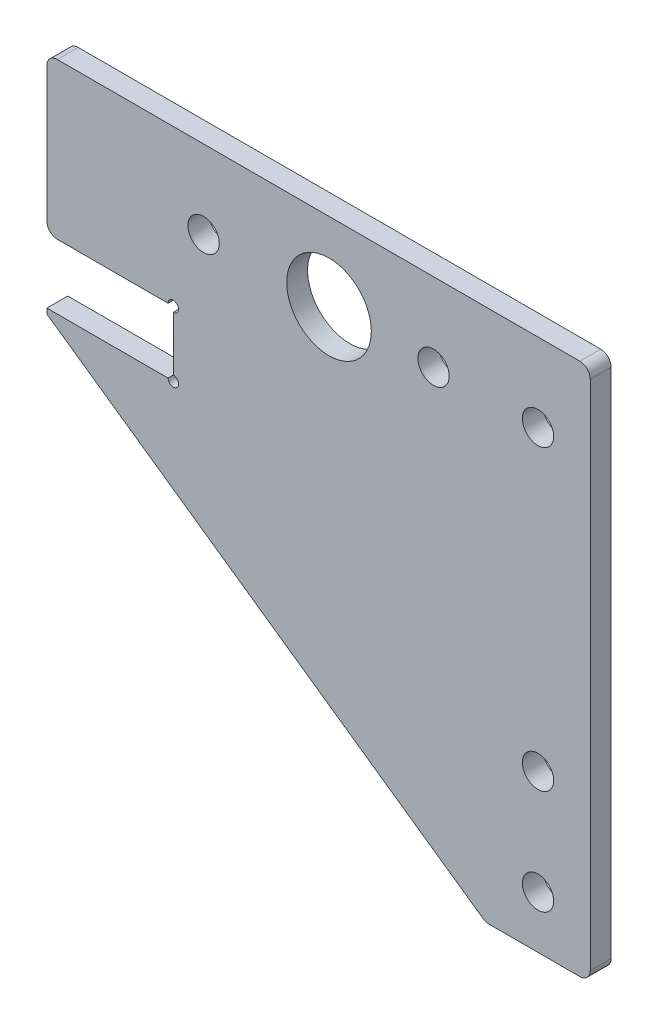
SolidWorks part; units mm, degrees
material "环氧板3240"
ref_plane "前视基准面" through (0, 0, 0) normal (0, 0, 1) x (1, 0, 0)
ref_plane "上视基准面" through (0, 0, 0) normal (0, 1, 0) x (1, 0, 0)
ref_plane "右视基准面" through (0, 0, 0) normal (1, 0, 0) x (0, 0, -1)
other "Configuration Table"
sketch "草图1" plane through (0, 0, 0) normal (0, 0, 1) x (1, 0, 0)
  line L1 (-5, -43.5) -> (5, -43.5)
  line L2 (5, -43.5) -> (5, 7.5)
  line L5 (-47, 7.5) -> (-47, -7.4)
  line L6 (-47, 0) -> (0, 0) construction
  line L7 (0, 0) -> (0, -43.5) construction
  line L9 (-47, -14.0913) -> (-5, -43.5)
  line L10 (-49.5736, -19.2913) -> (-15.2583, -43.3192) construction
  line L11 (-49.5736, -19.2913) -> (-15.2583, -43.3192) construction
  line L14 (-47, -7.4) -> (-34.9, -7.4)
  line L15 (5, 7.5) -> (-47, 7.5)
  line L16 (-34.9, -7.4) -> (-34.9, -13.6)
  line L17 (-34.9, -13.6) -> (-47, -13.6)
  line L18 (-47, -13.6) -> (-47, -14.0913)
  circle A0 centre (-32, 0) radius 1.5
  circle A4 centre (-10, 0) radius 1.5
  circle A5 centre (0, -28.5) radius 1.5
  circle A6 centre (0, 0) radius 1.5
  circle A10 centre (-20, 0) radius 4.05
  circle A11 centre (0, -38.5) radius 1.5
  dimension "D7" = 3
  dimension "D8" = 15
  dimension "D9" = 7.5
  dimension "D10" = 14.9
  dimension "D11" = 8.1
  dimension "D6" = 10
  dimension "D4" = 5
  dimension "D13" = 20
  dimension "D17" = 10
  dimension "D2" = 10
  dimension "D3" = 52
  dimension "D12" = 51
  dimension "D14" = 6.2
  dimension "D15" = 39.9
  dimension "D16" = 145
extrude "凸台-拉伸1" add sketch "草图1" along normal blind 2 contours L1 L2 L15 L5 L9
sketch "草图2" plane through (0, 0, 0) normal (0, 0, -1) x (-1, 0, 0)
  circle A0 centre (34.9, -7.4) radius 0.5
  circle A1 centre (34.9, -13.6) radius 0.5
  dimension "D1" = 1
extrude "切除-拉伸1" cut sketch "草图2" against normal blind 10
fillet "圆角1" radius 1 5 edges at (-5, -43.5, 1) (5, -43.5, 1) (5, 7.5, 1) (-47, -7.4, 1) (-47, 7.5, 1)
